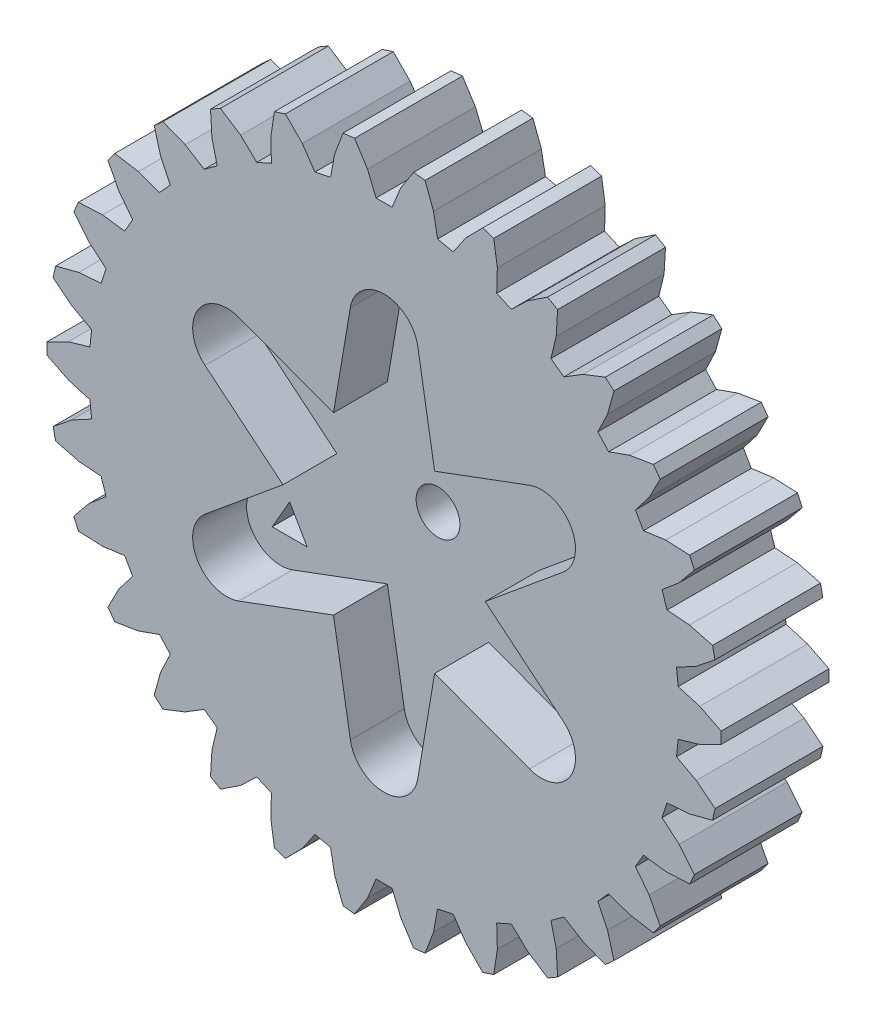
SolidWorks part; units mm, degrees
material "ABS"
ref_plane "Front Plane" through (0, 0, 0) normal (0, 0, 1) x (1, 0, 0)
ref_plane "Top Plane" through (0, 0, 0) normal (0, 1, 0) x (1, 0, 0)
ref_plane "Right Plane" through (0, 0, 0) normal (1, 0, 0) x (0, 0, -1)
sketch "Sketch1" plane through (0, 0, 0) normal (0, 0, 1) x (1, 0, 0)
  line L0 (67.8387, 65.5179) -> (69.435, 65.0497)
  line L1 (69.435, 65.0497) -> (71.0262, 64.252)
  line L2 (71.0262, 64.252) -> (71.0262, 63.394)
  line L3 (71.0262, 63.394) -> (69.435, 62.5962)
  line L4 (69.435, 62.5962) -> (67.8387, 62.1281)
  line L5 (67.8387, 62.1281) -> (67.7144, 60.9457)
  line L6 (67.7144, 60.9457) -> (69.1786, 60.156)
  line L7 (69.1786, 60.156) -> (70.5691, 59.0447)
  line L8 (70.5691, 59.0447) -> (70.3908, 58.2056)
  line L9 (70.3908, 58.2056) -> (68.6684, 57.756)
  line L10 (68.6684, 57.756) -> (67.0096, 57.6301)
  line L11 (67.0096, 57.6301) -> (66.6423, 56.4993)
  line L12 (66.6423, 56.4993) -> (67.9102, 55.4225)
  line L13 (67.9102, 55.4225) -> (69.0393, 54.0464)
  line L14 (69.0393, 54.0464) -> (68.6904, 53.2627)
  line L15 (68.6904, 53.2627) -> (66.9123, 53.181)
  line L16 (66.9123, 53.181) -> (65.2636, 53.4028)
  line L17 (65.2636, 53.4028) -> (64.669, 52.3732)
  line L18 (64.669, 52.3732) -> (65.6854, 51.0562)
  line L19 (65.6854, 51.0562) -> (66.5038, 49.4753)
  line L20 (66.5038, 49.4753) -> (65.9995, 48.7814)
  line L21 (65.9995, 48.7814) -> (64.2432, 49.0712)
  line L22 (64.2432, 49.0712) -> (62.6766, 49.6308)
  line L23 (62.6766, 49.6308) -> (61.8811, 48.7473)
  line L24 (61.8811, 48.7473) -> (62.6014, 47.2478)
  line L25 (62.6014, 47.2478) -> (63.0732, 45.5314)
  line L26 (63.0732, 45.5314) -> (62.4357, 44.9574)
  line L27 (62.4357, 44.9574) -> (60.778, 45.606)
  line L28 (60.778, 45.606) -> (59.3621, 46.4791)
  line L29 (59.3621, 46.4791) -> (58.4003, 45.7802)
  line L30 (58.4003, 45.7802) -> (58.793, 44.1638)
  line L31 (58.793, 44.1638) -> (58.8977, 42.3868)
  line L32 (58.8977, 42.3868) -> (58.1548, 41.9579)
  line L33 (58.1548, 41.9579) -> (56.6682, 42.9369)
  line L34 (56.6682, 42.9369) -> (55.4646, 44.0854)
  line L35 (55.4646, 44.0854) -> (54.3785, 43.6018)
  line L36 (54.3785, 43.6018) -> (54.4267, 41.939)
  line L37 (54.4267, 41.939) -> (54.1596, 40.1792)
  line L38 (54.1596, 40.1792) -> (53.3436, 39.914)
  line L39 (53.3436, 39.914) -> (52.0932, 41.1808)
  line L40 (52.0932, 41.1808) -> (51.1547, 42.5544)
  line L41 (51.1547, 42.5544) -> (49.9918, 42.3072)
  line L42 (49.9918, 42.3072) -> (49.6932, 40.6706)
  line L43 (49.6932, 40.6706) -> (49.066, 39.0048)
  line L44 (49.066, 39.0048) -> (48.2128, 38.9151)
  line L45 (48.2128, 38.9151) -> (47.253, 40.4142)
  line L46 (47.253, 40.4142) -> (46.6207, 41.9528)
  line L47 (46.6207, 41.9528) -> (45.4317, 41.9528)
  line L48 (45.4317, 41.9528) -> (44.7994, 40.4142)
  line L49 (44.7994, 40.4142) -> (43.8396, 38.9151)
  line L50 (43.8396, 38.9151) -> (42.9864, 39.0048)
  line L51 (42.9864, 39.0048) -> (42.3592, 40.6706)
  line L52 (42.3592, 40.6706) -> (42.0606, 42.3072)
  line L53 (42.0606, 42.3072) -> (40.8977, 42.5544)
  line L54 (40.8977, 42.5544) -> (39.9592, 41.1808)
  line L55 (39.9592, 41.1808) -> (38.7088, 39.914)
  line L56 (38.7088, 39.914) -> (37.8928, 40.1792)
  line L57 (37.8928, 40.1792) -> (37.6257, 41.939)
  line L58 (37.6257, 41.939) -> (37.6739, 43.6018)
  line L59 (37.6739, 43.6018) -> (36.5878, 44.0854)
  line L60 (36.5878, 44.0854) -> (35.3842, 42.9369)
  line L61 (35.3842, 42.9369) -> (33.8976, 41.9579)
  line L62 (33.8976, 41.9579) -> (33.1547, 42.3868)
  line L63 (33.1547, 42.3868) -> (33.2594, 44.1638)
  line L64 (33.2594, 44.1638) -> (33.6521, 45.7802)
  line L65 (33.6521, 45.7802) -> (32.6903, 46.4791)
  line L66 (32.6903, 46.4791) -> (31.2744, 45.606)
  line L67 (31.2744, 45.606) -> (29.6167, 44.9574)
  line L68 (29.6167, 44.9574) -> (28.9792, 45.5314)
  line L69 (28.9792, 45.5314) -> (29.451, 47.2478)
  line L70 (29.451, 47.2478) -> (30.1713, 48.7473)
  line L71 (30.1713, 48.7473) -> (29.3758, 49.6308)
  line L72 (29.3758, 49.6308) -> (27.8092, 49.0712)
  line L73 (27.8092, 49.0712) -> (26.0529, 48.7814)
  line L74 (26.0529, 48.7814) -> (25.5486, 49.4753)
  line L75 (25.5486, 49.4753) -> (26.367, 51.0562)
  line L76 (26.367, 51.0562) -> (27.3834, 52.3732)
  line L77 (27.3834, 52.3732) -> (26.7888, 53.4028)
  line L78 (26.7888, 53.4028) -> (25.1401, 53.181)
  line L79 (25.1401, 53.181) -> (23.362, 53.2627)
  line L80 (23.362, 53.2627) -> (23.0131, 54.0464)
  line L81 (23.0131, 54.0464) -> (24.1422, 55.4225)
  line L82 (24.1422, 55.4225) -> (25.4101, 56.4993)
  line L83 (25.4101, 56.4993) -> (25.0428, 57.6301)
  line L84 (25.0428, 57.6301) -> (23.384, 57.756)
  line L85 (23.384, 57.756) -> (21.6616, 58.2056)
  line L86 (21.6616, 58.2056) -> (21.4833, 59.0447)
  line L87 (21.4833, 59.0447) -> (22.8738, 60.156)
  line L88 (22.8738, 60.156) -> (24.338, 60.9457)
  line L89 (24.338, 60.9457) -> (24.2137, 62.1281)
  line L90 (24.2137, 62.1281) -> (22.6174, 62.5962)
  line L91 (22.6174, 62.5962) -> (21.0262, 63.394)
  line L92 (21.0262, 63.394) -> (21.0262, 64.252)
  line L93 (21.0262, 64.252) -> (22.6174, 65.0497)
  line L94 (22.6174, 65.0497) -> (24.2137, 65.5179)
  line L95 (24.2137, 65.5179) -> (24.338, 66.7003)
  line L96 (24.338, 66.7003) -> (22.8738, 67.49)
  line L97 (22.8738, 67.49) -> (21.4833, 68.6013)
  line L98 (21.4833, 68.6013) -> (21.6616, 69.4404)
  line L99 (21.6616, 69.4404) -> (23.384, 69.89)
  line L100 (23.384, 69.89) -> (25.0428, 70.0159)
  line L101 (25.0428, 70.0159) -> (25.4101, 71.1467)
  line L102 (25.4101, 71.1467) -> (24.1422, 72.2235)
  line L103 (24.1422, 72.2235) -> (23.0131, 73.5996)
  line L104 (23.0131, 73.5996) -> (23.362, 74.3832)
  line L105 (23.362, 74.3832) -> (25.1401, 74.465)
  line L106 (25.1401, 74.465) -> (26.7888, 74.2432)
  line L107 (26.7888, 74.2432) -> (27.3834, 75.2728)
  line L108 (27.3834, 75.2728) -> (26.367, 76.5898)
  line L109 (26.367, 76.5898) -> (25.5486, 78.1707)
  line L110 (25.5486, 78.1707) -> (26.0529, 78.8646)
  line L111 (26.0529, 78.8646) -> (27.8092, 78.5748)
  line L112 (27.8092, 78.5748) -> (29.3758, 78.0151)
  line L113 (29.3758, 78.0151) -> (30.1713, 78.8987)
  line L114 (30.1713, 78.8987) -> (29.451, 80.3982)
  line L115 (29.451, 80.3982) -> (28.9792, 82.1145)
  line L116 (28.9792, 82.1145) -> (29.6167, 82.6886)
  line L117 (29.6167, 82.6886) -> (31.2744, 82.04)
  line L118 (31.2744, 82.04) -> (32.6903, 81.1669)
  line L119 (32.6903, 81.1669) -> (33.6521, 81.8658)
  line L120 (33.6521, 81.8658) -> (33.2594, 83.4822)
  line L121 (33.2594, 83.4822) -> (33.1547, 85.2592)
  line L122 (33.1547, 85.2592) -> (33.8976, 85.6881)
  line L123 (33.8976, 85.6881) -> (35.3842, 84.7091)
  line L124 (35.3842, 84.7091) -> (36.5878, 83.5606)
  line L125 (36.5878, 83.5606) -> (37.6739, 84.0442)
  line L126 (37.6739, 84.0442) -> (37.6257, 85.707)
  line L127 (37.6257, 85.707) -> (37.8928, 87.4668)
  line L128 (37.8928, 87.4668) -> (38.7088, 87.732)
  line L129 (38.7088, 87.732) -> (39.9592, 86.4652)
  line L130 (39.9592, 86.4652) -> (40.8977, 85.0916)
  line L131 (40.8977, 85.0916) -> (42.0606, 85.3388)
  line L132 (42.0606, 85.3388) -> (42.3592, 86.9754)
  line L133 (42.3592, 86.9754) -> (42.9864, 88.6412)
  line L134 (42.9864, 88.6412) -> (43.8396, 88.7309)
  line L135 (43.8396, 88.7309) -> (44.7994, 87.2318)
  line L136 (44.7994, 87.2318) -> (45.4317, 85.6932)
  line L137 (45.4317, 85.6932) -> (46.6207, 85.6932)
  line L138 (46.6207, 85.6932) -> (47.253, 87.2318)
  line L139 (47.253, 87.2318) -> (48.2128, 88.7309)
  line L140 (48.2128, 88.7309) -> (49.066, 88.6412)
  line L141 (49.066, 88.6412) -> (49.6932, 86.9754)
  line L142 (49.6932, 86.9754) -> (49.9918, 85.3388)
  line L143 (49.9918, 85.3388) -> (51.1547, 85.0916)
  line L144 (51.1547, 85.0916) -> (52.0932, 86.4652)
  line L145 (52.0932, 86.4652) -> (53.3436, 87.732)
  line L146 (53.3436, 87.732) -> (54.1596, 87.4668)
  line L147 (54.1596, 87.4668) -> (54.4267, 85.707)
  line L148 (54.4267, 85.707) -> (54.3785, 84.0442)
  line L149 (54.3785, 84.0442) -> (55.4646, 83.5606)
  line L150 (55.4646, 83.5606) -> (56.6682, 84.7091)
  line L151 (56.6682, 84.7091) -> (58.1548, 85.6881)
  line L152 (58.1548, 85.6881) -> (58.8977, 85.2592)
  line L153 (58.8977, 85.2592) -> (58.793, 83.4822)
  line L154 (58.793, 83.4822) -> (58.4003, 81.8658)
  line L155 (58.4003, 81.8658) -> (59.3621, 81.1669)
  line L156 (59.3621, 81.1669) -> (60.778, 82.04)
  line L157 (60.778, 82.04) -> (62.4357, 82.6886)
  line L158 (62.4357, 82.6886) -> (63.0732, 82.1145)
  line L159 (63.0732, 82.1145) -> (62.6014, 80.3982)
  line L160 (62.6014, 80.3982) -> (61.8811, 78.8987)
  line L161 (61.8811, 78.8987) -> (62.6766, 78.0151)
  line L162 (62.6766, 78.0151) -> (64.2432, 78.5748)
  line L163 (64.2432, 78.5748) -> (65.9995, 78.8646)
  line L164 (65.9995, 78.8646) -> (66.5038, 78.1707)
  line L165 (66.5038, 78.1707) -> (65.6854, 76.5898)
  line L166 (65.6854, 76.5898) -> (64.669, 75.2728)
  line L167 (64.669, 75.2728) -> (65.2636, 74.2432)
  line L168 (65.2636, 74.2432) -> (66.9123, 74.465)
  line L169 (66.9123, 74.465) -> (68.6904, 74.3832)
  line L170 (68.6904, 74.3832) -> (69.0393, 73.5996)
  line L171 (69.0393, 73.5996) -> (67.9102, 72.2235)
  line L172 (67.9102, 72.2235) -> (66.6423, 71.1467)
  line L173 (66.6423, 71.1467) -> (67.0096, 70.0159)
  line L174 (67.0096, 70.0159) -> (68.6684, 69.89)
  line L175 (68.6684, 69.89) -> (70.3908, 69.4404)
  line L176 (70.3908, 69.4404) -> (70.5691, 68.6013)
  line L177 (70.5691, 68.6013) -> (69.1786, 67.49)
  line L178 (69.1786, 67.49) -> (67.7144, 66.7003)
  line L179 (67.7144, 66.7003) -> (67.8387, 65.5179)
  line L180 (48.6394, 38.96) -> (43.413, 88.686) construction
  line L181 (21.0262, 63.823) -> (71.0262, 63.823) construction
  point P184 (46.0262, 63.823)
sketch "Sketch3" plane through (0, 0, 0) normal (0, 0, 1) x (1, 0, 0)
  circle A0 centre (46.0262, 63.823) radius 18
  dimension "D1" = 36
sketch "Sketch4" plane through (0, 0, 0) normal (0, 0, 1) x (1, 0, 0)
  line L0 (42.2762, 70.3182) -> (46.0262, 63.823) construction
  line L1 (48.6394, 38.96) -> (43.413, 88.686) construction
  line L2 (46.0262, 63.823) -> (46.0262, 79.823) construction
  line L3 (42.2762, 70.3182) -> (43.5262, 77.7103)
  line L4 (49.7762, 70.3182) -> (48.5262, 77.7103)
  line L5 (46.0262, 63.823) -> (49.7762, 70.3182) construction
  line L6 (49.7762, 70.3182) -> (56.8029, 72.9317)
  line L7 (53.5262, 63.823) -> (59.3029, 68.6016)
  line L8 (53.5262, 63.823) -> (59.3029, 59.0444)
  line L9 (49.7762, 57.3278) -> (56.8029, 54.7143)
  line L10 (49.7762, 57.3278) -> (48.5262, 49.9357)
  line L11 (42.2762, 57.3278) -> (43.5262, 49.9357)
  line L12 (42.2762, 57.3278) -> (35.2495, 54.7143)
  line L13 (38.5262, 63.823) -> (32.7495, 59.0444)
  line L14 (38.5262, 63.823) -> (32.7495, 68.6016)
  line L15 (42.2762, 70.3182) -> (35.2495, 72.9317)
  arc A0 (48.5262, 77.7103) -> (43.5262, 77.7103) centre (46.0262, 77.2875) ccw
  circle A1 centre (46.0262, 63.823) radius 7.5 construction
  arc A2 (59.3029, 68.6016) -> (56.8029, 72.9317) centre (57.6868, 70.5553) ccw
  circle A3 centre (46.0262, 63.823) radius 7.5 construction
  arc A4 (56.8029, 54.7143) -> (59.3029, 59.0444) centre (57.6868, 57.0907) ccw
  circle A5 centre (46.0262, 63.823) radius 7.5 construction
  arc A6 (43.5262, 49.9357) -> (48.5262, 49.9357) centre (46.0262, 50.3585) ccw
  circle A7 centre (46.0262, 63.823) radius 7.5 construction
  arc A8 (32.7495, 59.0444) -> (35.2495, 54.7143) centre (34.3656, 57.0907) ccw
  circle A9 centre (46.0262, 63.823) radius 7.5 construction
  arc A10 (35.2495, 72.9317) -> (32.7495, 68.6016) centre (34.3656, 70.5553) ccw
  circle A11 centre (46.0262, 63.823) radius 7.5 construction
  point P0 (46.0262, 63.823)
  point P43 (46.0262, 63.823)
  dimension "D1" = 16
  dimension "D3" = 7.5
  dimension "D4" = 5
extrude "Boss-Extrude1" add sketch "Sketch1" against normal blind 8
sketch "Sketch5" plane through (0, 0, 0) normal (0, 0, 1) x (1, 0, 0)
  circle A0 centre (46.0262, 63.823) radius 1.625
  point P0 (46.0262, 63.823)
  dimension "D1" = 3.25
sketch "Sketch7" plane through (0, 0, -8) normal (0, 0, -1) x (-1, 0, 0)
  circle A0 centre (-46.0262, 63.823) radius 2.875
  point P0 (-46.0262, 63.823)
  dimension "D1" = 5.75
extrude "Cut-Extrude4" cut sketch "Sketch4" against normal blind 4
extrude "Cut-Extrude5" cut sketch "Sketch5" against normal through all
extrude "Cut-Extrude6" cut sketch "Sketch7" against normal blind 1.5
sketch "Sketch9" plane through (0, 0, 0) normal (0, 0, 1) x (1, 0, 0)
  line L0 (46.0262, 63.823) -> (46.0262, 81.823) construction
  line L1 (57.0247, 58.973) -> (55.7257, 56.723)
  line L2 (47.3252, 75.773) -> (46.0262, 78.023)
  line L3 (46.0262, 78.023) -> (44.7272, 75.773)
  line L4 (44.7272, 75.773) -> (47.3252, 75.773)
  line L5 (55.7257, 56.723) -> (58.3238, 56.723)
  line L6 (58.3238, 56.723) -> (57.0247, 58.973)
  line L7 (46.0262, 63.823) -> (61.6147, 54.823) construction
  line L8 (36.3267, 56.723) -> (35.0277, 58.973)
  line L9 (35.0277, 58.973) -> (33.7286, 56.723)
  line L10 (33.7286, 56.723) -> (36.3267, 56.723)
  line L11 (46.0262, 63.823) -> (30.4377, 54.823) construction
  circle A0 centre (46.0262, 63.823) radius 18 construction
  circle A1 centre (46.0262, 76.523) radius 0.75 construction
  point P0 (46.0262, 63.823)
  point P22 (46.0262, 63.823)
  dimension "D1" = 1.5
  dimension "D2" = 12.7
  dimension "D3" = 3
extrude "Cut-Extrude7" cut sketch "Sketch9" against normal through all
